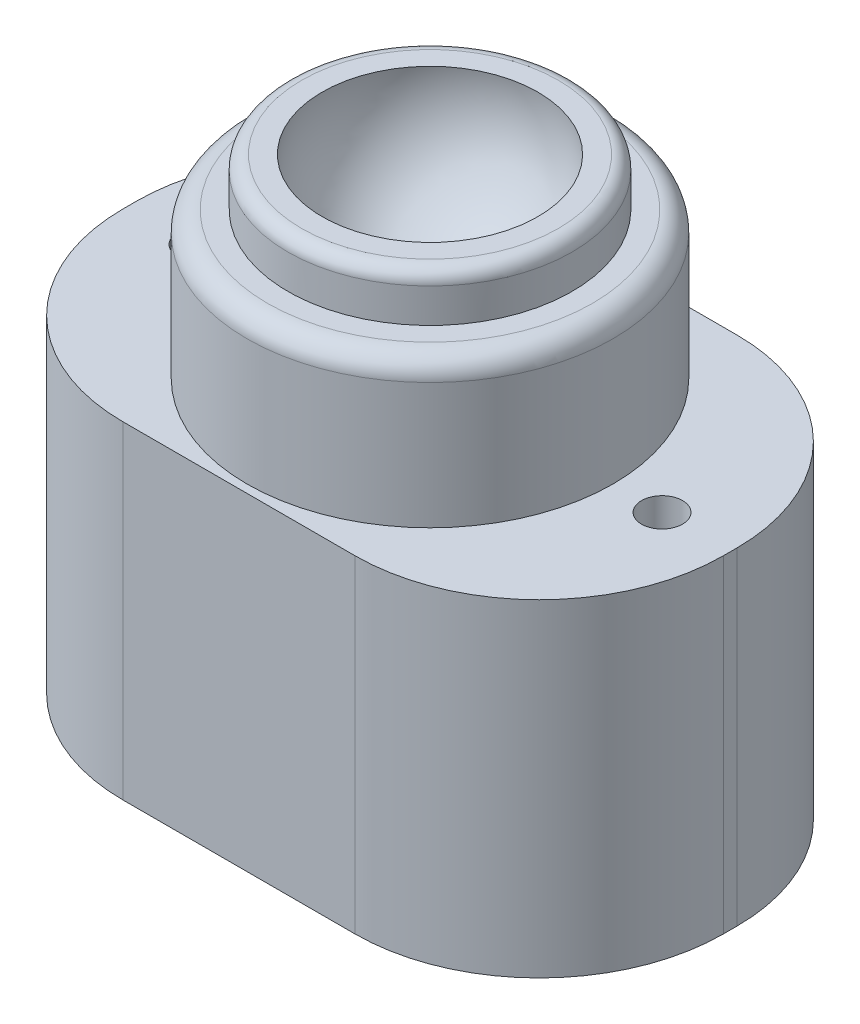
SolidWorks part; units mm, degrees
ref_plane "Front Plane" through (0, 0, 0) normal (0, 0, 1) x (1, 0, 0)
ref_plane "Top Plane" through (0, 0, 0) normal (0, 1, 0) x (1, 0, 0)
ref_plane "Right Plane" through (0, 0, 0) normal (1, 0, 0) x (0, 0, -1)
sketch "Sketch1" plane through (0, 0, 0) normal (0, 0, 1) x (1, 0, 0)
  line L0 (0, 0) -> (0, 5)
  line L3 (7.907, 14.2157) -> (10.407, 14.2157)
  line L4 (10.407, 14.2157) -> (10.407, 10.7157)
  line L5 (10.407, 10.7157) -> (13.407, 10.7157)
  line L6 (13.407, 10.7157) -> (13.407, 0)
  line L7 (13.407, 0) -> (0, 0)
  arc A0 (7.907, 14.2157) -> (0, 5) centre (-0.0001, 13) cw
  dimension "D2" = 8
  dimension "D1" = 5
  dimension "D3" = 2.5
  dimension "D4" = 3
  dimension "D5" = 3.5
  dimension "D6" = 13.407
revolve "Revolve2" add sketch "Sketch1" angle 360 about L0
fillet "Fillet1" radius 1 1 edges at (0, 14.2157, -10.407)
fillet "Fillet2" radius 1.5 1 edges at (0, 10.7157, -13.407)
sketch "Sketch5" plane through (0, 0, 0) normal (0, 1, 0) x (1, 0, 0)
  line L12 (22, -14) -> (-22, -14)
  line L13 (22, -14) -> (22, 14)
  line L14 (22, 14) -> (-22, 14)
  line L15 (-22, -14) -> (-22, 14)
  line L16 (22, -14) -> (-22, 14) construction
  line L17 (22, 14) -> (-22, -14) construction
  point P0 (0, 0)
  dimension "D1" = 28
  dimension "D2" = 44
extrude "Boss-Extrude1" add sketch "Sketch5" against normal blind 24
fillet "Fillet3" radius 13.5 4 edges at (22, -12, 14) (22, -12, -14) (-22, -12, -14) (-22, -12, 14)
sketch "Sketch7" plane through (0, 0, 0) normal (0, 1, 0) x (1, 0, 0)
  line L0 (8.5, 14) -> (-8.5, 14) construction
  line L1 (-22, 0.5) -> (-22, -0.5) construction
  circle A0 centre (-17, 0) radius 1.5
  dimension "D1" = 3
  dimension "D2" = 14
  dimension "D3" = 5
extrude "Cut-Extrude1" cut sketch "Sketch7" against normal through all
ref_plane "Plane1" through (0, 0, 0) normal (-1, 0, 0) x (0, 0, 1)
mirror "Mirror1" about plane through (0, 0, 0) normal (-1, 0, 0) of "Cut-Extrude1"
